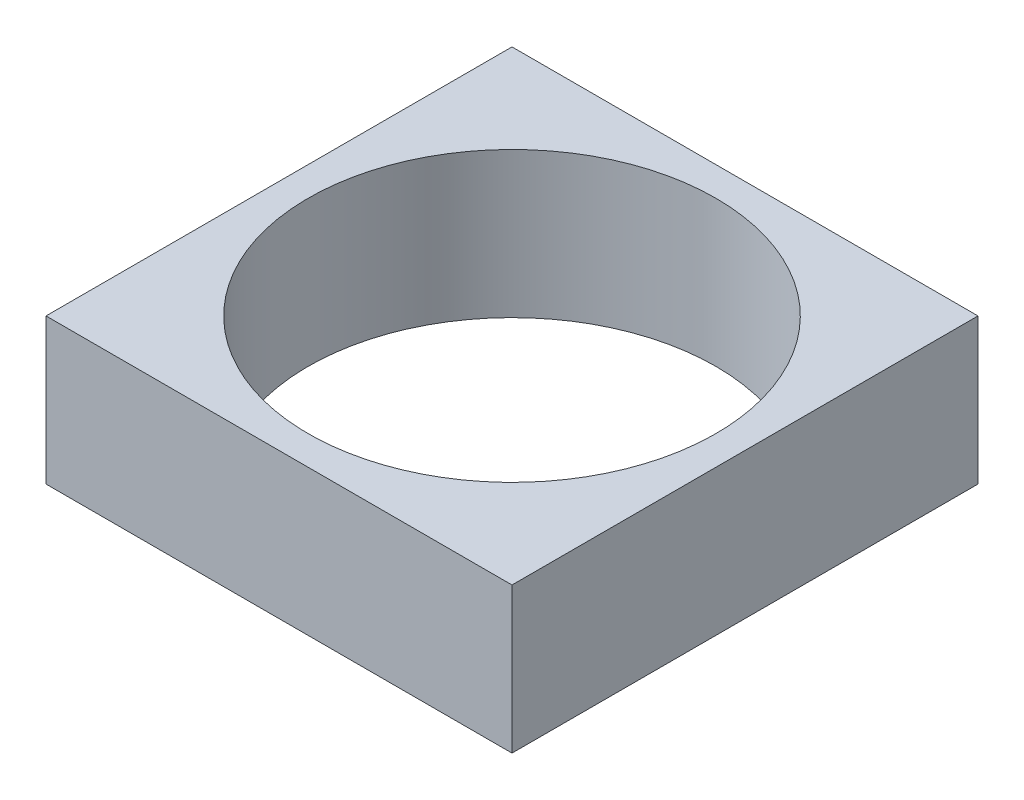
SolidWorks part; units mm, degrees
ref_plane "Front Plane" through (0, 0, 0) normal (0, 0, 1) x (1, 0, 0)
ref_plane "Top Plane" through (0, 0, 0) normal (0, 1, 0) x (1, 0, 0)
ref_plane "Right Plane" through (0, 0, 0) normal (1, 0, 0) x (0, 0, -1)
sketch "Sketch1" plane through (0, 0, 0) normal (0, 1, 0) x (1, 0, 0)
  line L1 (-40, 40) -> (40, 40)
  line L2 (-40, 40) -> (-40, -40)
  line L3 (-40, -40) -> (40, -40)
  line L4 (40, 40) -> (40, -40)
  line L5 (-40, 40) -> (40, -40) construction
  line L6 (-40, -40) -> (40, 40) construction
  point P0 (0, 0)
  dimension "D1" = 80
  dimension "D2" = 80
extrude "Boss-Extrude1" add sketch "Sketch1" along normal blind 25
sketch "Sketch2" plane through (0, 0, 0) normal (0, -1, 0) x (1, 0, 0)
  circle A0 centre (0, 0) radius 35
  dimension "D1" = 70
extrude "Cut-Extrude1" cut sketch "Sketch2" against normal through all
